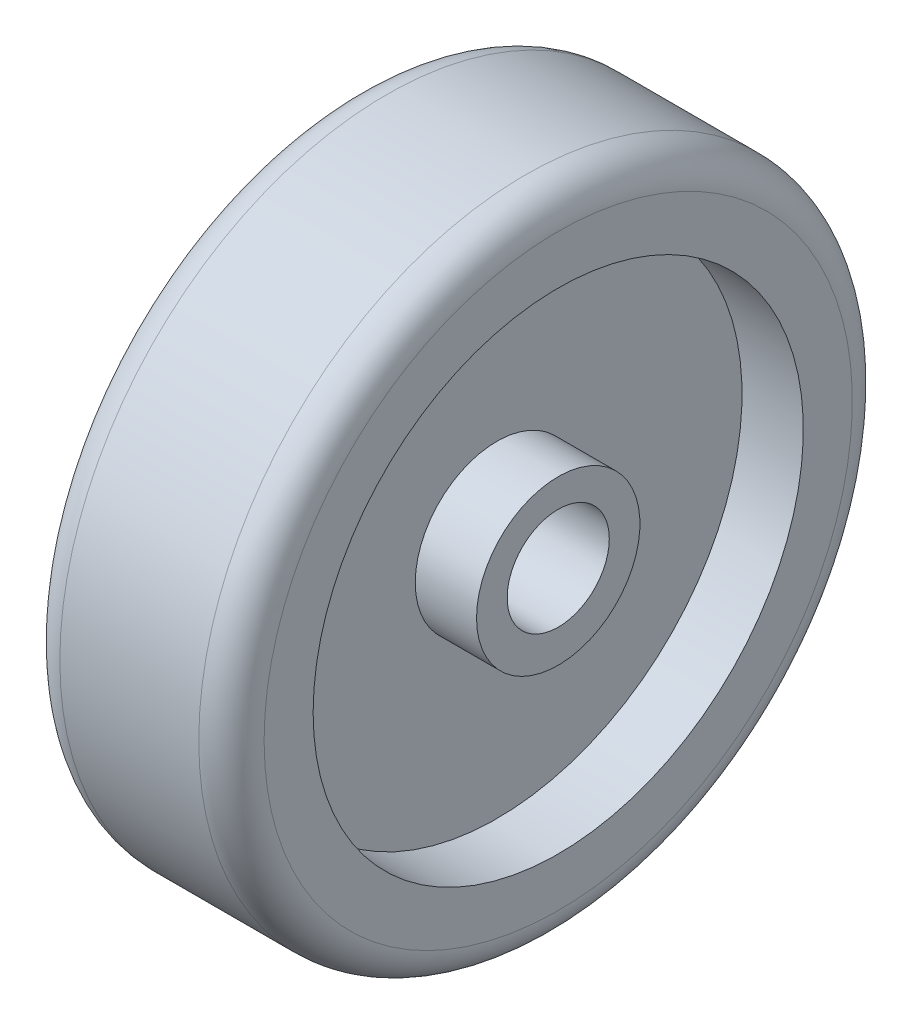
SolidWorks part; units mm, degrees
ref_plane "Front Plane" through (0, 0, 0) normal (0, 0, 1) x (1, 0, 0)
ref_plane "Top Plane" through (0, 0, 0) normal (0, 1, 0) x (1, 0, 0)
ref_plane "Right Plane" through (0, 0, 0) normal (1, 0, 0) x (0, 0, -1)
sketch "Sketch1" plane through (0, 0, 0) normal (0, 0, 1) x (1, 0, 0)
  line L0 (0, 0) -> (0, 88.0925) construction
  line L1 (0, 0) -> (-72.3706, 0) construction
  line L2 (-31.75, -0.7295) -> (-31.75, 24.6705)
  line L3 (-31.75, 24.6705) -> (-12.7, 24.6705)
  line L4 (-12.7, 24.6705) -> (-12.7, 75.4705)
  line L5 (-12.7, 75.4705) -> (-31.75, 75.4705)
  line L6 (-31.75, 75.4705) -> (-31.75, 100.8705)
  line L7 (31.75, 75.4705) -> (31.75, 100.8705)
  line L8 (12.7, 75.4705) -> (31.75, 75.4705)
  line L9 (12.7, 24.6705) -> (12.7, 75.4705)
  line L10 (31.75, 24.6705) -> (12.7, 24.6705)
  line L11 (31.75, -0.7295) -> (31.75, 24.6705)
  line L12 (-31.75, 100.8705) -> (31.75, 100.8705)
  line L13 (-31.75, -0.7295) -> (31.75, -0.7295)
  dimension "D1" = 63.5
  dimension "D2" = 63.5
  dimension "D3" = 25.4
  dimension "D4" = 50.8
  dimension "D5" = 25.4
  dimension "D6" = 25.4
revolve "Revolve2" add sketch "Sketch1" angle 360 about L13
sketch "Sketch2" plane through (31.75, 0, 0) normal (1, 0, 0) x (0, 0, -1)
  circle A0 centre (0, 0) radius 15.875
  dimension "D1" = 31.75
extrude "Cut-Extrude1" cut sketch "Sketch2" against normal through all
fillet "Fillet2" radius 10.16 1 edges at (31.75, -0.7295, 101.6)
fillet "Fillet3" radius 10.16 1 edges at (-31.75, -0.7295, 101.6)
